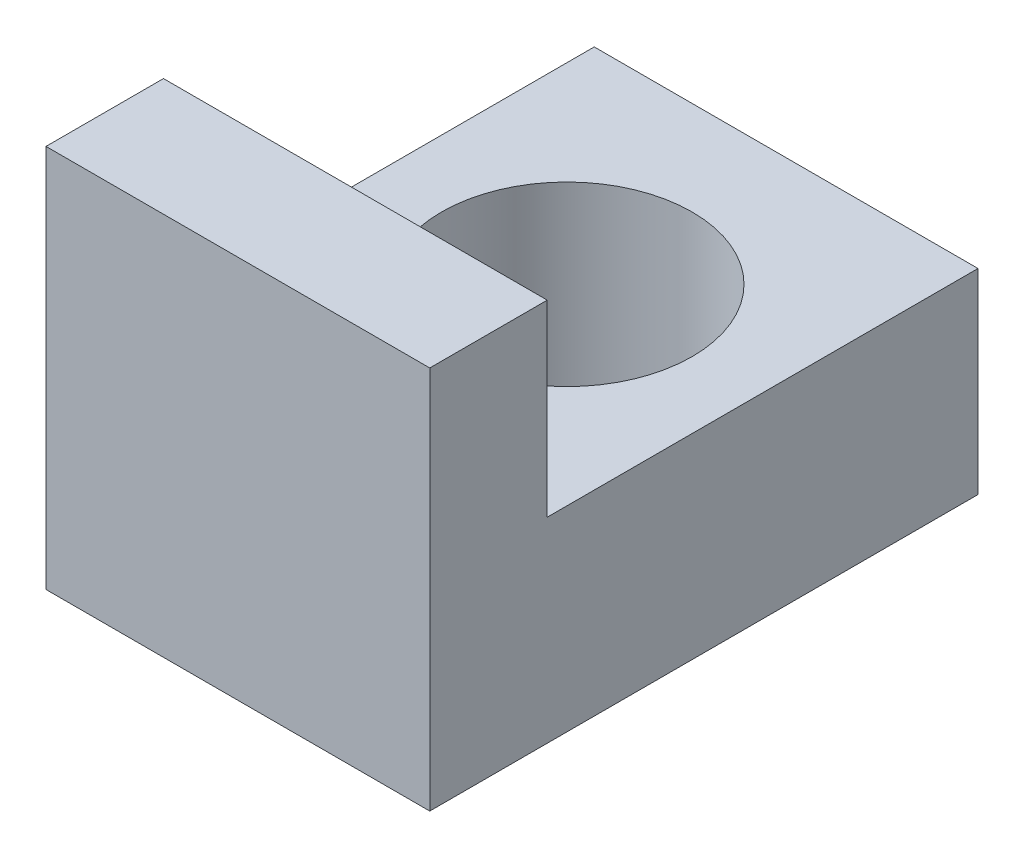
SolidWorks part; units mm, degrees
ref_plane "Front Plane" through (0, 0, 0) normal (0, 0, 1) x (1, 0, 0)
ref_plane "Top Plane" through (0, 0, 0) normal (0, 1, 0) x (1, 0, 0)
ref_plane "Right Plane" through (0, 0, 0) normal (1, 0, 0) x (0, 0, -1)
sketch "Sketch1" plane through (0, 0, 0) normal (1, 0, 0) x (0, 0, -1)
  line L0 (0, 0) -> (0, 4.9)
  line L1 (0, 4.9) -> (1.5, 4.9)
  line L2 (1.5, 4.9) -> (1.5, 2.5)
  line L3 (1.5, 2.5) -> (7, 2.5)
  line L4 (7, 2.5) -> (7, 0)
  line L5 (7, 0) -> (0, 0)
  dimension "D1" = 4.9
  dimension "D2" = 2.5
  dimension "D3" = 7
  dimension "D4" = 1.5
extrude "Boss-Extrude1" add sketch "Sketch1" along normal blind 4.9
sketch "Sketch2" plane through (0, 0, 0) normal (0, -1, 0) x (1, 0, 0)
  line L0 (2.45, 0) -> (2.45, -8.4721) construction
  line L1 (4.9, 0) -> (0, 0) construction
  circle A0 centre (2.45, -4.2) radius 1.6
  dimension "D1" = 3.2
  dimension "D2" = 4.2
extrude "Cut-Extrude1" cut sketch "Sketch2" against normal through all
